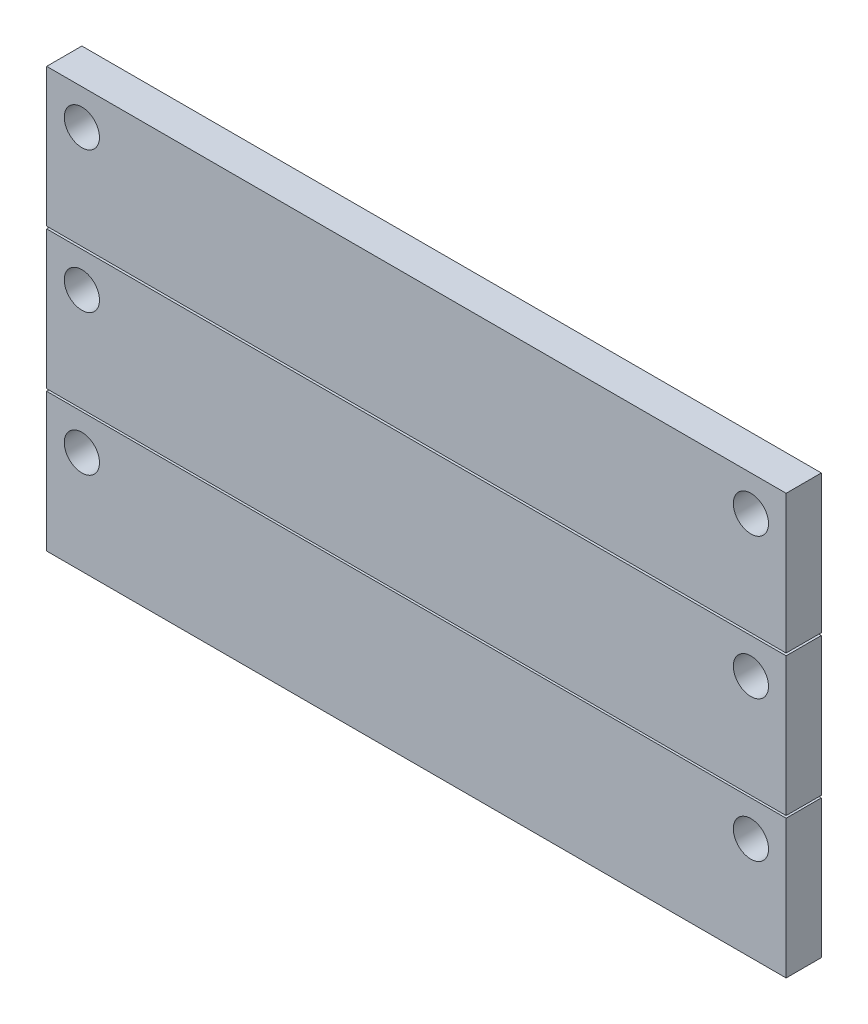
SolidWorks part; units mm, degrees
ref_plane "Front Plane" through (0, 0, 0) normal (0, 0, 1) x (1, 0, 0)
ref_plane "Top Plane" through (0, 0, 0) normal (0, 1, 0) x (1, 0, 0)
ref_plane "Right Plane" through (0, 0, 0) normal (1, 0, 0) x (0, 0, -1)
sketch "Sketch1" plane through (0, 0, 0) normal (0, 0, 1) x (1, 0, 0)
  line L0 (0, 0) -> (-533.4, 0)
  line L1 (-533.4, 0) -> (-533.4, -99.822)
  line L2 (-533.4, -99.822) -> (0, -99.822)
  line L3 (0, -99.822) -> (0, 0)
  line L4 (0, 101.5397) -> (-533.4, 101.5397)
  line L5 (-533.4, 101.5397) -> (-533.4, 1.7177)
  line L6 (-533.4, 1.7177) -> (0, 1.7177)
  line L7 (0, 1.7177) -> (0, 101.5397)
  line L12 (0, -101.4458) -> (-533.4, -101.4458)
  line L13 (-533.4, -101.4458) -> (-533.4, -201.2678)
  line L14 (-533.4, -201.2678) -> (0, -201.2678)
  line L15 (0, -201.2678) -> (0, -101.4458)
  dimension "D1" = 90
  dimension "D2" = 533.4
  dimension "D3" = 99.822
extrude "Boss-Extrude1" add sketch "Sketch1" along normal blind 25.4
sketch "Sketch2" plane through (0, 0, 25.4) normal (0, 0, 1) x (1, 0, 0)
  line L0 (-533.4, 0) -> (-533.4, -99.822) construction
  line L2 (-266.7, 101.5397) -> (-266.7, -298.1217) construction
  line L3 (0, 101.5397) -> (-533.4, 101.5397) construction
  circle A0 centre (-508, 76.1397) radius 12.7
  circle A1 centre (-25.4, 76.1397) radius 12.7
  dimension "D1" = 25.4
  dimension "D2" = 25.4
  dimension "D3" = 25.4
extrude "Cut-Extrude1" cut sketch "Sketch2" against normal through all
pattern_linear "LPattern1" count 3 spacing 101.6 along (0, -1, 0) of "Cut-Extrude1"
